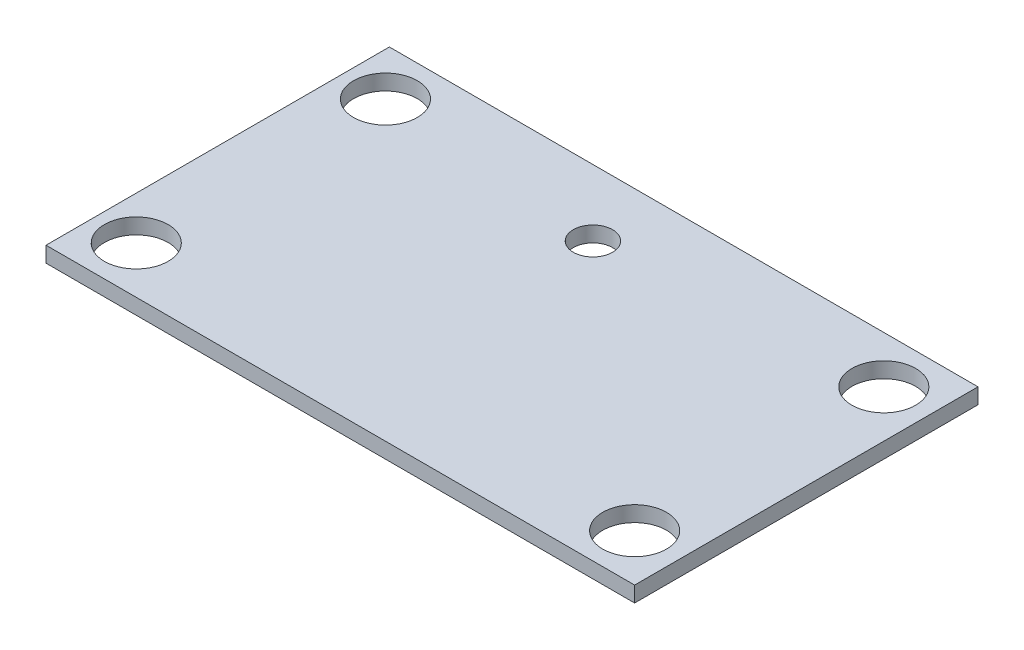
SolidWorks part; units mm, degrees
ref_plane "Front Plane" through (0, 0, 0) normal (0, 0, 1) x (1, 0, 0)
ref_plane "Top Plane" through (0, 0, 0) normal (0, 1, 0) x (1, 0, 0)
ref_plane "Right Plane" through (0, 0, 0) normal (1, 0, 0) x (0, 0, -1)
sketch "Sketch1" plane through (0, 0, 0) normal (0, 1, 0) x (1, 0, 0)
  line L1 (-30, -17.5) -> (30, -17.5)
  line L2 (-30, -17.5) -> (-30, 17.5)
  line L3 (-30, 17.5) -> (30, 17.5)
  line L4 (30, -17.5) -> (30, 17.5)
  line L5 (-30, -17.5) -> (30, 17.5) construction
  line L6 (-30, 17.5) -> (30, -17.5) construction
  circle A0 centre (-25.6, 12.7) radius 3.25
  circle A1 centre (25.2, 12.7) radius 3.25
  circle A2 centre (-25.6, -12.7) radius 3.25
  circle A3 centre (25.2, -12.7) radius 3.25
  point P0 (0, 0)
  dimension "D4" = 6.5
  dimension "D5" = 6.5
  dimension "D9" = 6.5
  dimension "D10" = 6.5
  dimension "D1" = 60
  dimension "D2" = 35
  dimension "D3" = 50.8
  dimension "D6" = 25.4
  dimension "D13" = 4.8
  dimension "D14" = 4.8
extrude "Boss-Extrude1" add sketch "Sketch1" along normal blind 1.5875
sketch "Sketch2" plane through (0, 1.5875, 0) normal (0, 1, 0) x (1, 0, 0)
  line L2 (-30, 17.5) -> (-30, -17.5) construction
  line L4 (30, 17.5) -> (-30, 17.5) construction
  circle A0 centre (-2.5, 10.75) radius 2
  dimension "D1" = 4
  dimension "D2" = 6.75
  dimension "D3" = 27.5
extrude "Cut-Extrude1" cut sketch "Sketch2" against normal through all
